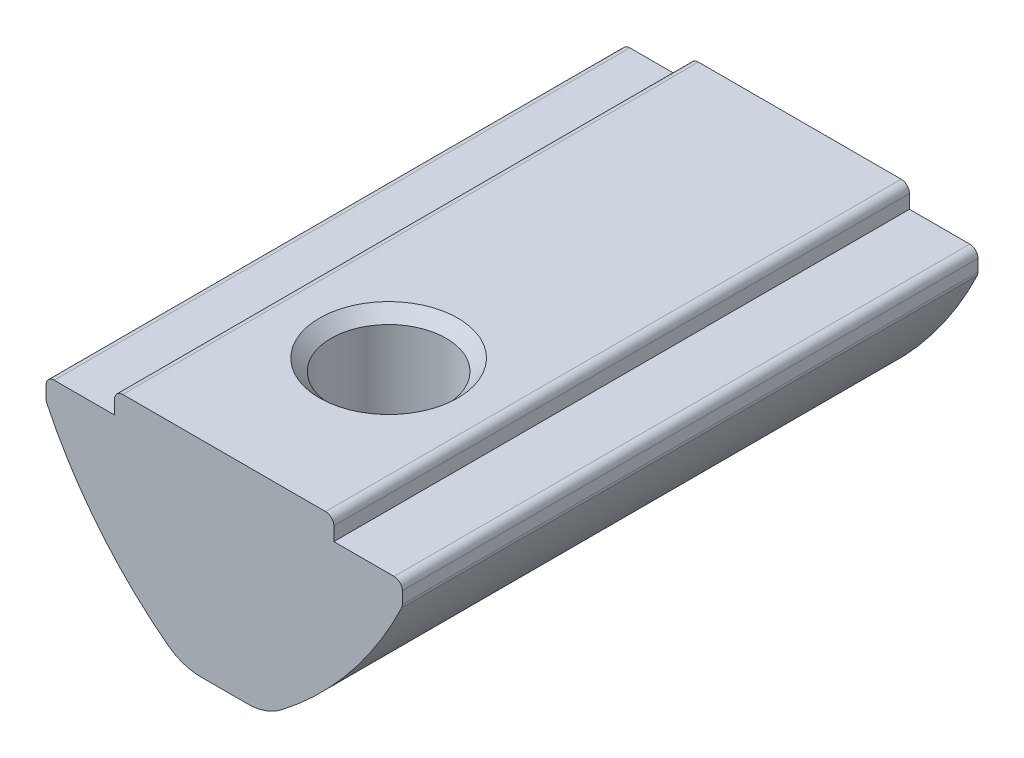
SolidWorks part; units mm, degrees
ref_plane "Спереди" through (0, 0, 0) normal (0, 0, 1) x (1, 0, 0)
ref_plane "Сверху" through (0, 0, 0) normal (0, 1, 0) x (1, 0, 0)
ref_plane "Справа" through (0, 0, 0) normal (1, 0, 0) x (0, 0, -1)
sketch "Эскиз1" plane through (0, 0, 0) normal (0, 0, 1) x (1, 0, 0)
  line L0 (-4, 0) -> (4, 0)
  line L5 (-4, 0) -> (-4, -0.8)
  line L6 (-4, -0.8) -> (-6.5, -0.8)
  line L7 (-6.5, -0.8) -> (-6.5, -1.6)
  line L8 (4, 0) -> (4, -0.8)
  line L9 (4, -0.8) -> (6.5, -0.8)
  line L10 (6.5, -0.8) -> (6.5, -1.6)
  line L11 (-1.5, -7.5) -> (1.5, -7.5)
  arc A0 (-6.5, -1.6) -> (-1.5, -7.5) centre (7.0567, 4.82) ccw
  arc A1 (1.5, -7.5) -> (6.5, -1.6) centre (-7.0567, 4.82) ccw
  point P0 (0, -7.5)
  point P4 (0, 0)
  dimension "D7" = 15
  dimension "D1" = 8
  dimension "D2" = 13
  dimension "D3" = 0.8
  dimension "D4" = 3
  dimension "D5" = 0.8
  dimension "D6" = 7.5
extrude "Бобышка-Вытянуть1" add sketch "Эскиз1" along normal mid plane 21
fillet "Скругление1" radius 0.3 6 edges at (6.5, -1.6, 0) (6.5, -0.8, 0) (-6.5, -0.8, 0) (-6.5, -1.6, 0) (4, 0, 0) (-4, 0, 0)
fillet "Скругление2" radius 2 2 edges at (1.5, -7.5, 0) (-1.5, -7.5, 0)
hole_wizard "Отверстие обработанное метчиком M52" positions "Эскиз2" profile "Эскиз4" tap size "M5" standard "ISO" end condition through all
sketch "Эскиз2" plane through (0, 0, 0) normal (0, 1, 0) x (1, 0, 0)
  line L0 (3.7, -10.5) -> (-3.7, -10.5) construction
  point P0 (0, -4.5)
  dimension "D1" = 6
sketch "Эскиз4" plane through (0, 0, 4.5) normal (1, 0, 0) x (0, 0, 1)
  line L0 (0, 0) -> (0, 7.5)
  line L1 (0, 7.5) -> (2.1, 7.5)
  line L2 (2.1, 7.5) -> (2.1, 0.425)
  line L3 (2.1, 0.425) -> (2.525, 0)
  line L5 (2.525, 0) -> (0, 0)
  line L6 (-2.1, 0.425) -> (-2.525, 0) construction
  line L11 (0, -6.35) -> (0, 107.95) construction
  dimension "Диаметр проходного сверла" = 4.2
  dimension "Глубина проходного сверла" = 7.5
  dimension "Диаметр передней зенковки" = 5.05
  dimension "Угол передней зенковки" = 90
cosmetic thread "Отверстие резьбы1" parameters "D2"=5
sketch "Эскиз5" plane through (0, 0, 0) normal (1, 0, 0) x (0, 0, -1)
  line L1 (6.5, -4.3) -> (6.5, -8.3) construction
  line L2 (10.5, -7.0877) -> (10.5, -1.6618) construction
  line L3 (6.5, -4.3) -> (6.5, -8.3)
  line L5 (10.5, -7.5) -> (-2.5792, -7.5) construction
  arc A0 (6.5, -4.3) -> (6.5, -8.3) centre (6.5, -6.3) ccw
  point P3 (4, -7.4722)
  dimension "D3" = 2
  dimension "D1" = 0.8
  dimension "D2" = 4
revolve "Повернуть1" add sketch "Эскиз5" angle 360 about L1
